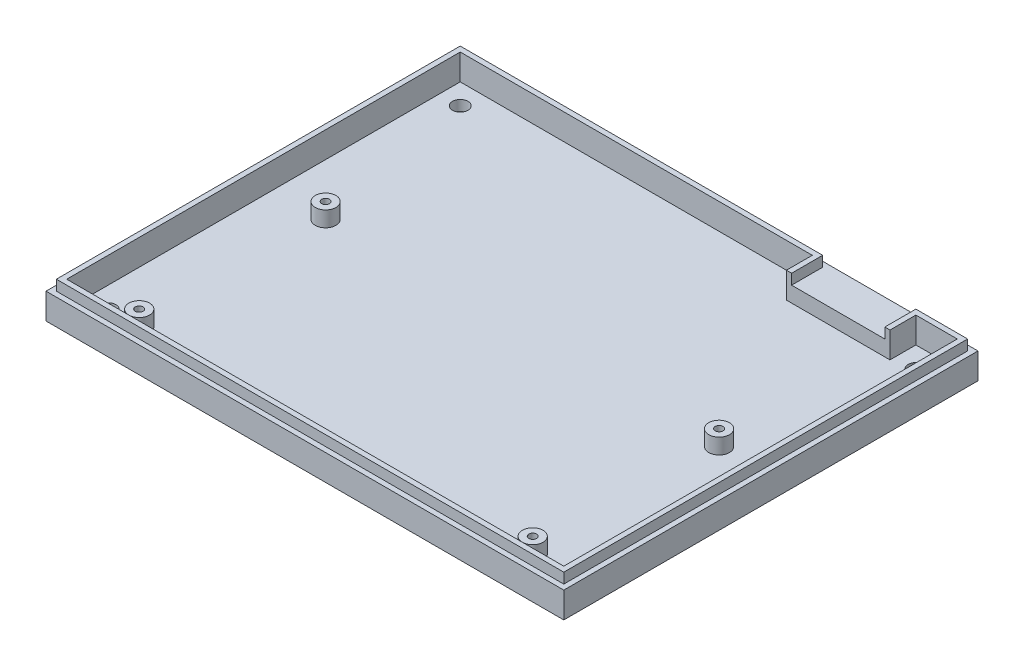
SolidWorks part; units mm, degrees
ref_plane "Plan de face" through (0, 0, 0) normal (0, 0, 1) x (1, 0, 0)
ref_plane "Plan de dessus" through (0, 0, 0) normal (0, 1, 0) x (1, 0, 0)
ref_plane "Plan de droite" through (0, 0, 0) normal (1, 0, 0) x (0, 0, -1)
sketch "Esquisse1" plane through (0, 0, 0) normal (0, 1, 0) x (1, 0, 0)
  line L1 (50, 40) -> (-50, 40)
  line L2 (50, 40) -> (50, -40)
  line L3 (50, -40) -> (-50, -40)
  line L4 (-50, 40) -> (-50, -40)
  line L5 (50, 40) -> (-50, -40) construction
  line L6 (50, -40) -> (-50, 40) construction
  point P0 (0, 0)
  dimension "D1" = 100
  dimension "D2" = 80
extrude "Boss.-Extru.1" add sketch "Esquisse1" along normal blind 2
sketch "Esquisse2" plane through (0, 2, 0) normal (0, 1, 0) x (1, 0, 0)
  line L0 (-48, 38) -> (-48, -38)
  line L1 (-48, -38) -> (48, -38)
  line L2 (48, -38) -> (48, 38)
  line L3 (48, 38) -> (-48, 38)
  line L4 (-50, 40) -> (-50, -40)
  line L5 (-50, -40) -> (50, -40)
  line L6 (50, -40) -> (50, 40)
  line L7 (50, 40) -> (-50, 40)
  line L8 (-50, 40) -> (-50, -40)
  line L9 (-50, -40) -> (50, -40)
  line L10 (50, -40) -> (50, 40)
  line L11 (50, 40) -> (-50, 40)
  line L12 (0, 0) -> (0, -38) construction
  line L14 (40, -36) -> (-40, -36) construction
  line L15 (40, -36) -> (40, 4) construction
  line L16 (40, 4) -> (-40, 4) construction
  line L17 (-40, -36) -> (-40, 4) construction
  line L18 (40, -36) -> (-40, 4) construction
  line L19 (40, 4) -> (-40, -36) construction
  circle A0 centre (-38, 2) radius 2
  circle A1 centre (-38, -34) radius 2
  circle A2 centre (38, 2) radius 2
  circle A3 centre (38, -34) radius 2
  point P11 (0, -16)
  line M10 (-50, 40) -> (-50, -40)
  line M11 (-50, -40) -> (50, -40)
  line M12 (50, -40) -> (50, 40)
  line M13 (50, 40) -> (-50, 40)
  dimension "D6" = 4
  dimension "D7" = 4
  dimension "D8" = 4
  dimension "D9" = 4
  dimension "D3" = 40
  dimension "D4" = 80
  dimension "D5" = 4
  dimension "D1" = 0
  dimension "D2" = 2
extrude "Boss.-Extru.2" add sketch "Esquisse2" along normal blind 3 contours L3 L2 L1 L0 M13 M10 M11 M12 | A3 | A2 | A1 | A0
sketch "Esquisse3" plane through (0, 5, 0) normal (0, 1, 0) x (1, 0, 0)
  circle A21 centre (-38, 2) radius 0.75
  circle A22 centre (-38, -34) radius 0.75
  circle A23 centre (38, 2) radius 0.75
  circle A24 centre (38, -34) radius 0.75
  dimension "D1" = 1.5
  dimension "D2" = 1.5
  dimension "D3" = 1.5
  dimension "D4" = 1.5
extrude "Enlèv. mat.-Extru.1" cut sketch "Esquisse3" against normal blind 5
sketch "Esquisse4" plane through (0, 2, 0) normal (0, 1, 0) x (1, 0, 0)
  line L0 (0, 0) -> (0, 38) construction
  line L1 (48, 38) -> (-48, 38) construction
  line L2 (0, 0) -> (48, 0) construction
  line L3 (48, -38) -> (48, 38) construction
  line L4 (48, 38) -> (-48, 38) construction
  line L5 (-48, 38) -> (-48, -38) construction
  circle A0 centre (-44, 34) radius 1.5
  circle A1 centre (44, 34) radius 1.5
  circle A2 centre (44, -34) radius 1.5
  circle A3 centre (-44, -34) radius 1.5
  dimension "D1" = 3
  dimension "D2" = 4
  dimension "D3" = 4
extrude "Enlèv. mat.-Extru.2" cut sketch "Esquisse4" against normal blind 5
sketch "Esquisse5" plane through (0, 5, 0) normal (0, 1, 0) x (1, 0, 0)
  line L4 (-48, -38) -> (48, -38) construction
  line L5 (48, -38) -> (48, 38) construction
  line L6 (-48, 38) -> (-48, -38) construction
  line L7 (48, 38) -> (-48, 38) construction
  line L8 (49, -39) -> (49, 39)
  line L9 (-49, -39) -> (49, -39)
  line L10 (-49, 39) -> (-49, -39)
  line L11 (49, 39) -> (-49, 39)
  line L12 (49, -39) -> (49, 39)
  line L13 (-49, -39) -> (49, -39)
  line L14 (-49, 39) -> (-49, -39)
  line L15 (49, 39) -> (-49, 39)
  line L16 (-48, -38) -> (48, -38)
  line L17 (48, -38) -> (48, 38)
  line L18 (-48, 38) -> (-48, -38)
  line L19 (48, 38) -> (-48, 38)
  dimension "D1" = 1
extrude "Boss.-Extru.3" add sketch "Esquisse5" along normal blind 2
sketch "Esquisse6" plane through (0, 2, 0) normal (0, 1, 0) x (1, 0, 0)
  line L0 (20, 38) -> (40, 38)
  line L1 (48, 38) -> (-48, 38) construction
  line L2 (40, 38) -> (40, 33)
  line L3 (40, 33) -> (20, 33)
  line L4 (20, 33) -> (20, 38)
  line L5 (50, -40) -> (50, 40) construction
  dimension "D1" = 10
  dimension "D2" = 20
  dimension "D3" = 5
extrude "Boss.-Extru.4" add sketch "Esquisse6" along normal blind 3
sketch "Esquisse7" plane through (0, 5, 0) normal (0, 1, 0) x (1, 0, 0)
  line L0 (20, 33) -> (20, 38)
  line L1 (40, 38) -> (20, 38) construction
  line L2 (20, 38) -> (20, 33) construction
  line L3 (20, 38) -> (21, 38)
  line L4 (21, 38) -> (21, 33)
  line L5 (20, 33) -> (40, 33) construction
  line L6 (21, 33) -> (20, 33)
  line L7 (30, 33) -> (30, 38) construction
  line L8 (39, 33) -> (40, 33)
  line L9 (39, 38) -> (39, 33)
  line L10 (40, 38) -> (39, 38)
  line L11 (40, 33) -> (40, 38)
  dimension "D1" = 1
extrude "Boss.-Extru.5" add sketch "Esquisse7" along normal blind 2
sketch "Esquisse8" plane through (0, 0, -38) normal (0, 0, 1) x (1, 0, 0)
  line L1 (21, 5) -> (39, 5)
  line L2 (21, 5) -> (21, 7)
  line L3 (21, 7) -> (39, 7)
  line L4 (39, 5) -> (39, 7)
  line L5 (21, 5) -> (39, 7) construction
  line L6 (21, 7) -> (39, 5) construction
  point P4 (30, 6)
extrude "Enlèv. mat.-Extru.3" cut sketch "Esquisse8" against normal blind 2
